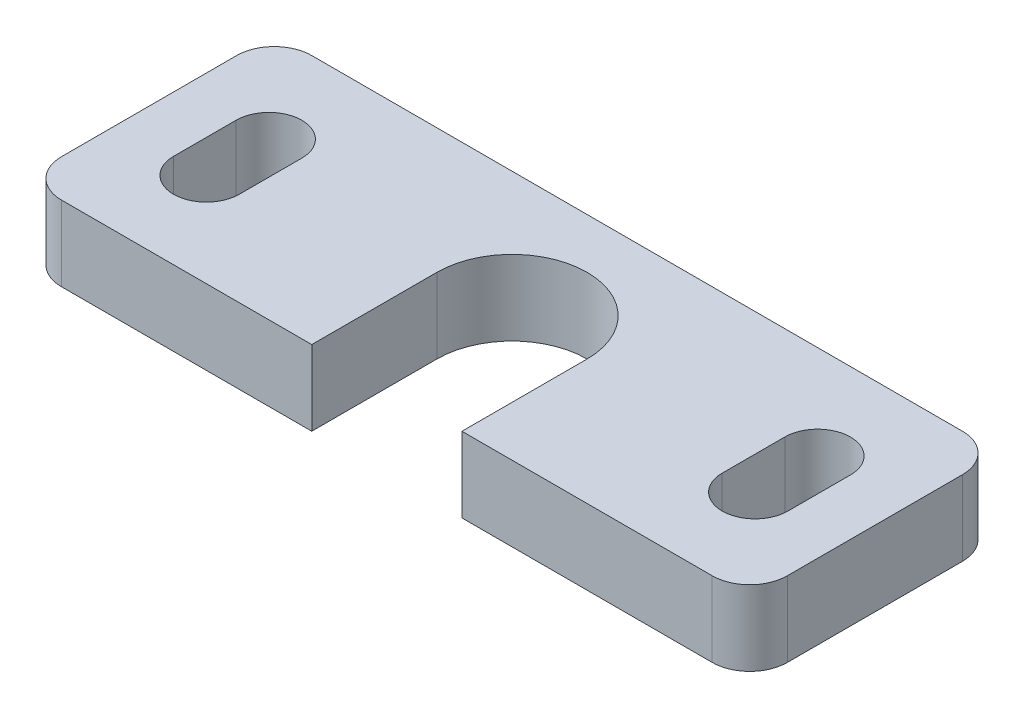
SolidWorks part; units mm, degrees
ref_plane "Front Plane" through (0, 0, 0) normal (0, 0, 1) x (1, 0, 0)
ref_plane "Top Plane" through (0, 0, 0) normal (0, 1, 0) x (1, 0, 0)
ref_plane "Right Plane" through (0, 0, 0) normal (1, 0, 0) x (0, 0, -1)
sketch "Sketch1" plane through (0, 0, 0) normal (0, 1, 0) x (1, 0, 0)
  line L0 (29, 20) -> (29, 0) construction
  line L1 (0, 0) -> (23, 0)
  line L2 (0, 0) -> (0, 20)
  line L3 (0, 20) -> (58, 20)
  line L4 (58, 0) -> (58, 20)
  line L5 (0, 0) -> (58, 20) construction
  line L6 (0, 20) -> (58, 0) construction
  line L7 (23, 0) -> (23, 10)
  line L8 (35, 10) -> (35, 0)
  line L9 (7.08, 12.5) -> (7.08, 7.5) construction
  line L10 (9.705, 12.5) -> (9.705, 7.5)
  line L11 (4.455, 12.5) -> (4.455, 7.5)
  line L12 (50.92, 12.5) -> (50.92, 7.5) construction
  line L13 (48.295, 12.5) -> (48.295, 7.5)
  line L14 (53.545, 12.5) -> (53.545, 7.5)
  line L15 (35, 0) -> (58, 0)
  arc A0 (23, 10) -> (35, 10) centre (29, 10) cw
  arc A1 (9.705, 12.5) -> (4.455, 12.5) centre (7.08, 12.5) ccw
  arc A2 (4.455, 7.5) -> (9.705, 7.5) centre (7.08, 7.5) ccw
  arc A3 (48.295, 12.5) -> (53.545, 12.5) centre (50.92, 12.5) cw
  arc A4 (53.545, 7.5) -> (48.295, 7.5) centre (50.92, 7.5) cw
  point P4 (29, 10)
  point P15 (7.08, 10)
  point P22 (50.92, 10)
  dimension "D4" = 6
  dimension "D5" = 2.625
  dimension "D1" = 58
  dimension "D2" = 20
  dimension "D3" = 10
  dimension "D6" = 10
  dimension "D7" = 43.84
  dimension "D8" = 5
extrude "Boss-Extrude1" add sketch "Sketch1" along normal blind 6
fillet "Fillet1" radius 3 4 edges at (0, 3, -20) (0, 3, 0) (58, 3, 0) (58, 3, -20)
